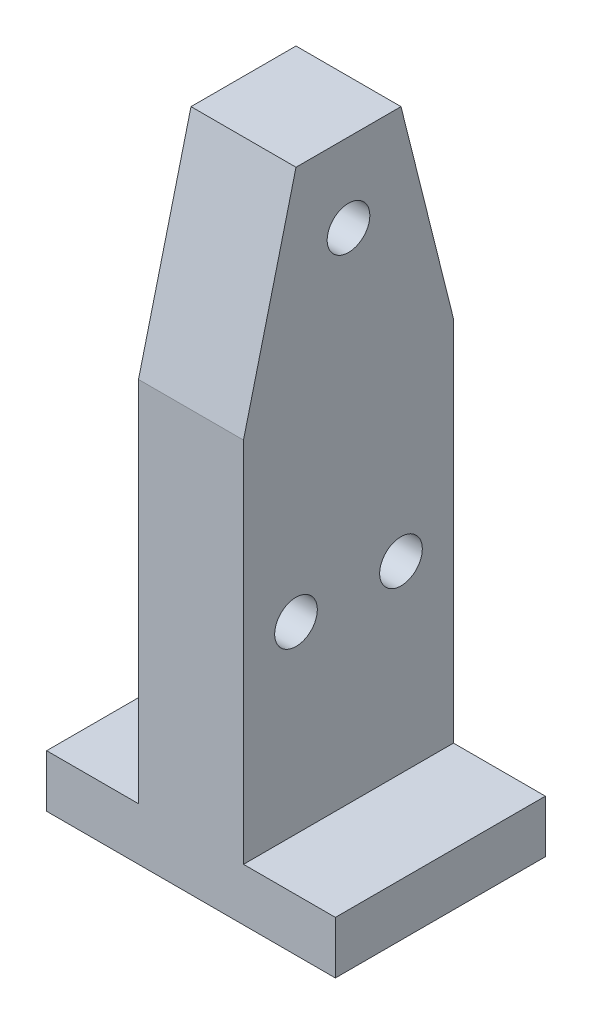
SolidWorks part; units mm, degrees
ref_plane "Front Plane" through (0, 0, 0) normal (0, 0, 1) x (1, 0, 0)
ref_plane "Top Plane" through (0, 0, 0) normal (0, 1, 0) x (1, 0, 0)
ref_plane "Right Plane" through (0, 0, 0) normal (1, 0, 0) x (0, 0, -1)
sketch "Sketch27" plane through (0, 0, 0) normal (0, 0, 1) x (1, 0, 0)
  line L0 (28.575, -69.85) -> (28.575, 76.2) construction
  line L1 (-34.925, -76.2) -> (34.925, -76.2)
  line L2 (-34.925, -76.2) -> (-34.925, 76.2)
  line L3 (-34.925, 76.2) -> (34.925, 76.2)
  line L4 (34.925, -76.2) -> (34.925, 76.2)
  line L5 (-34.925, -76.2) -> (34.925, 76.2) construction
  line L6 (-34.925, 76.2) -> (34.925, -76.2) construction
  line L7 (-28.575, -69.85) -> (28.575, -69.85) construction
  line L8 (-28.575, -69.85) -> (-28.575, 76.2) construction
  line L9 (28.575, -69.85) -> (28.575, 76.2) construction
  line L10 (-28.575, -69.85) -> (-28.575, 76.2) construction
  point P0 (0, 0)
  dimension "D2" = 57.15
  dimension "D3" = 152.4
  dimension "D1" = 6.35
extrude "Boss-Extrude4" add sketch "Sketch27" along normal mid plane 50.8
sketch "Sketch28" plane through (0, 0, 0) normal (0, 0, 1) x (1, 0, 0)
  line L3 (0, 0) -> (0, 76.2) construction
  line L6 (34.925, 76.2) -> (12.7, 76.2)
  line L7 (34.925, 76.2) -> (34.925, -63.5)
  line L8 (34.925, -63.5) -> (12.7, -63.5)
  line L9 (12.7, 76.2) -> (12.7, -63.5)
  line L10 (34.925, 76.2) -> (12.7, -63.5) construction
  line L11 (34.925, -63.5) -> (12.7, 76.2) construction
  line L12 (34.925, 76.2) -> (-34.925, 76.2) construction
  line L13 (-34.925, -76.2) -> (34.925, -76.2) construction
  point P4 (23.8125, 6.35)
  point P11 (8.4593, -53.1726)
  point P12 (12.7, -65.7104)
  dimension "D1" = 25.4
  dimension "D2" = 12.7
extrude "Cut-Extrude5" cut sketch "Sketch28" against normal through all both and the other way through all
mirror "Mirror1" about plane through (0, 0, 0) normal (1, 0, 0) of "Cut-Extrude5"
sketch "Sketch30" plane through (0, 0, 0) normal (1, 0, 0) x (0, 0, -1)
  line L0 (0, -76.2) -> (0, 76.2) construction
  line L1 (-25.4, -76.2) -> (-25.4, -63.5) construction
  line L2 (0, -76.2) -> (0, 76.2) construction
  line L3 (-25.4, 25.4) -> (-25.4, -76.2)
  line L4 (0, -69.85) -> (0, 76.2) construction
  line L5 (0, -76.2) -> (0, 76.2) construction
  line L6 (12.7, 76.2) -> (-12.7, 76.2)
  line L7 (-25.4, 76.2) -> (25.4, 76.2) construction
  line L8 (-12.7, 76.2) -> (-25.4, 25.4)
  line L10 (12.7, 76.2) -> (25.4, 25.4)
  line L11 (-25.4, -76.2) -> (25.4, -76.2)
  line L12 (25.4, -76.2) -> (25.4, 25.4)
  line L13 (-25.4, -76.2) -> (25.4, -76.2) construction
  dimension "D1" = 25.4
  dimension "D2" = 50.8
extrude "Cut-Extrude6" cut sketch "Sketch30" against normal through all both and the other way through all flip side to cut
sketch "Sketch32" plane through (0, 0, 0) normal (1, 0, 0) x (0, 0, -1)
  line L0 (0, 57.15) -> (-25.4, 82.55) construction
  line L1 (0, -69.85) -> (0, 76.2) construction
  line L2 (-12.7, 76.2) -> (12.7, 76.2) construction
  dimension "D1" = 25.4
  dimension "D2" = 25.4
  dimension "D3" = 19.05
sketch "Sketch38" plane through (-34.925, 0, 0) normal (-1, 0, 0) x (0, 0, 1)
  line L0 (0, 57.15) -> (25.4, 82.55) construction
  line L1 (5.5796, 76.2) -> (25.4, 96.0204)
  line L2 (12.7, 76.2) -> (-12.7, 76.2) construction
  line L3 (25.4, 82.55) -> (32.1352, 75.8148) construction
  line L4 (25.4, 96.0204) -> (38.8704, 82.55)
  line L5 (38.8704, 82.55) -> (16.6641, 60.3437)
  line L6 (12.7, 76.2) -> (50.8, -76.2) construction
  line L7 (25.4, 82.55) -> (18.6648, 89.2852) construction
  line L8 (25.4, 82.55) -> (32.1352, 89.2852) construction
  line L9 (5.5796, 76.2) -> (16.6641, 60.3437)
  dimension "D1" = 9.525
extrude "Boss-Extrude6" [suppressed] add sketch "Sketch38" against normal up to surface (6.35 mm away)
hole_wizard "3/8 Clearance Hole4" positions "Sketch39" profile "Sketch40" hole size "3/8" standard "ANSI Inch" end condition through all
sketch "Sketch39" plane through (-34.925, 0, 0) normal (-1, 0, 0) x (0, 0, 1)
  point P0 (25.4, 82.55)
  point P3 (0, 57.15)
sketch "Sketch40" plane through (-34.925, 82.55, 25.4) normal (0, 1, 0) x (0, 0, 1)
  line L0 (0, 0) -> (0, 69.85)
  line L1 (0, 69.85) -> (5.1587, 69.85)
  line L2 (5.1587, 69.85) -> (5.1587, 0)
  line L5 (5.1587, 0) -> (0, 0)
  line L11 (0, -6.35) -> (0, 107.95) construction
  dimension "Thru Hole Dia." = 10.3175
  dimension "Thru Hole Depth" = 69.85
draft "Draft1" [suppressed] type of draft neutral plane draft angle 5 faces to draft 2 parameters "D1"=5
hole_wizard "Auxiliary Mounting Holes" positions "Sketch42" profile "Sketch43" hole size "3/8" standard "ANSI Inch" end condition through all
sketch "Sketch42" plane through (12.7, 0, 0) normal (1, 0, 0) x (0, 0, -1)
  line L0 (12.7, -19.05) -> (-12.7, -19.05) construction
  circle A0 centre (0, 57.15) radius 5.1587 construction
  point P0 (-12.7, -19.05)
  point P2 (12.7, -19.05)
  point P10 (11.0273, -23.7162)
  point P11 (0, -19.05)
  point P13 (13.1421, -34.2903)
  point P16 (9.9699, -19.05)
  dimension "D1" = 76.2
  dimension "D2" = 25.4
sketch "Sketch43" plane through (12.7, -19.05, 12.7) normal (0, 1, 0) x (0, 0, -1)
  line L0 (0, 0) -> (0, 47.625)
  line L1 (0, 47.625) -> (5.1587, 47.625)
  line L2 (5.1587, 47.625) -> (5.1587, 0)
  line L5 (5.1587, 0) -> (0, 0)
  line L11 (0, -6.35) -> (0, 107.95) construction
  dimension "Thru Hole Dia." = 10.3175
  dimension "Thru Hole Depth" = 47.625
